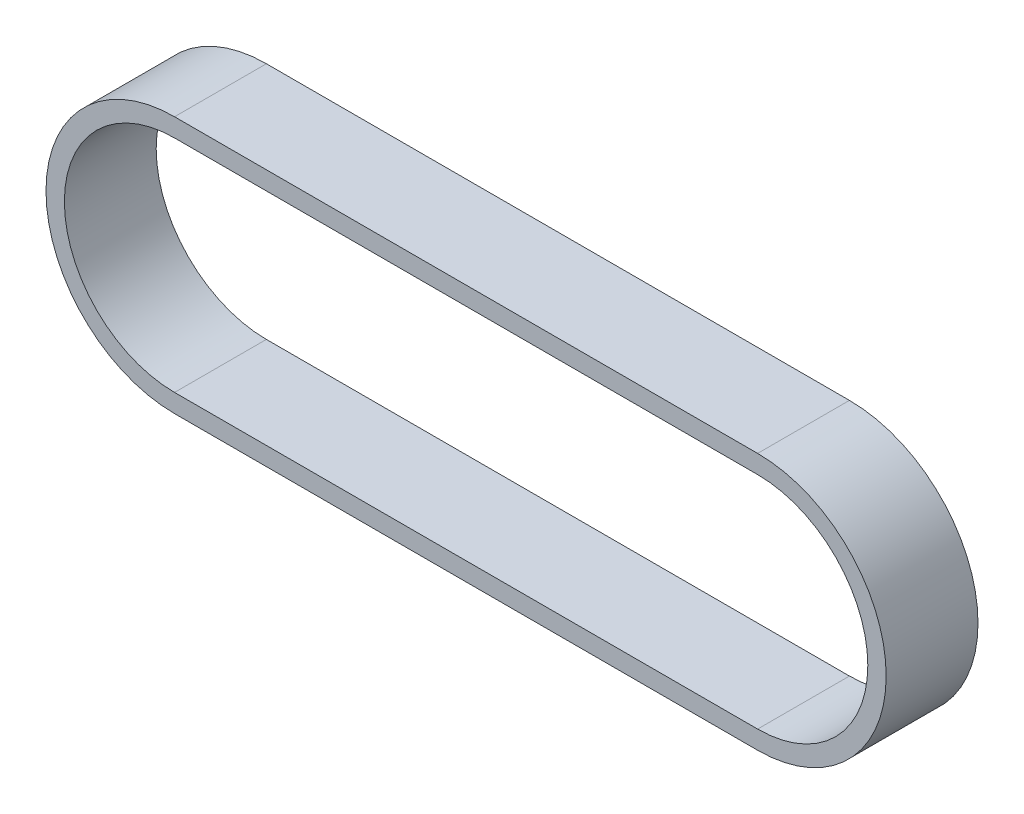
SolidWorks part; units mm, degrees
ref_plane "前视基准面" through (0, 0, 0) normal (0, 0, 1) x (1, 0, 0)
ref_plane "上视基准面" through (0, 0, 0) normal (0, 1, 0) x (1, 0, 0)
ref_plane "右视基准面" through (0, 0, 0) normal (1, 0, 0) x (0, 0, -1)
other "Configuration Table"
sketch "草图1" plane through (0, 0, 0) normal (0, 0, 1) x (1, 0, 0)
  line L0 (0, 0) -> (63.5, 0) construction
  line L1 (0, 14) -> (63.5, 14)
  line L2 (0, -14) -> (63.5, -14)
  line L3 (0, 12) -> (63.5, 12)
  line L4 (0, -12) -> (63.5, -12)
  arc A0 (0, 14) -> (0, -14) centre (0, 0) ccw
  arc A1 (63.5, -14) -> (63.5, 14) centre (63.5, 0) ccw
  arc A2 (63.5, -12) -> (63.5, 12) centre (63.5, 0) ccw
  arc A3 (0, 12) -> (0, -12) centre (0, 0) ccw
  point P3 (31.75, 0)
  dimension "D2" = 14
  dimension "D1" = 63.5
  dimension "D3" = 2
extrude "凸台-拉伸1" add sketch "草图1" along normal blind 10
